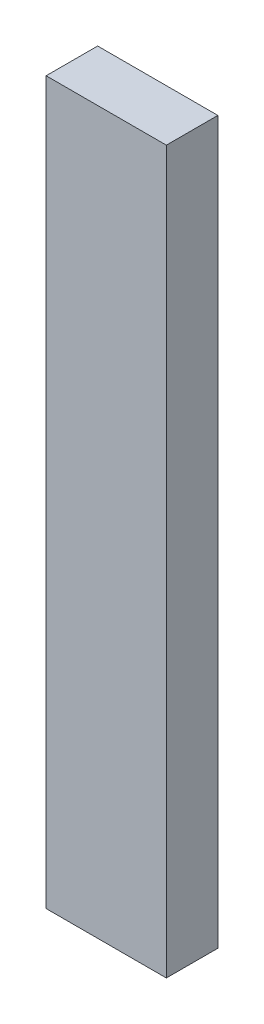
SolidWorks part; units mm, degrees
material "Oak"
ref_plane "Front Plane" through (0, 0, 0) normal (0, 0, 1) x (1, 0, 0)
ref_plane "Top Plane" through (0, 0, 0) normal (0, 1, 0) x (1, 0, 0)
ref_plane "Right Plane" through (0, 0, 0) normal (1, 0, 0) x (0, 0, -1)
sketch "Sketch1" plane through (0, 0, 0) normal (0, 1, 0) x (1, 0, 0)
  line L1 (-44.45, -19.05) -> (44.45, -19.05)
  line L2 (-44.45, -19.05) -> (-44.45, 19.05)
  line L3 (-44.45, 19.05) -> (44.45, 19.05)
  line L4 (44.45, -19.05) -> (44.45, 19.05)
  line L5 (-44.45, -19.05) -> (44.45, 19.05) construction
  line L6 (-44.45, 19.05) -> (44.45, -19.05) construction
  point P0 (0, 0)
  dimension "D1" = 38.1
  dimension "D2" = 88.9
extrude "Boss-Extrude1" add sketch "Sketch1" along normal blind 533.4 contours L3 L4 L1 L2
